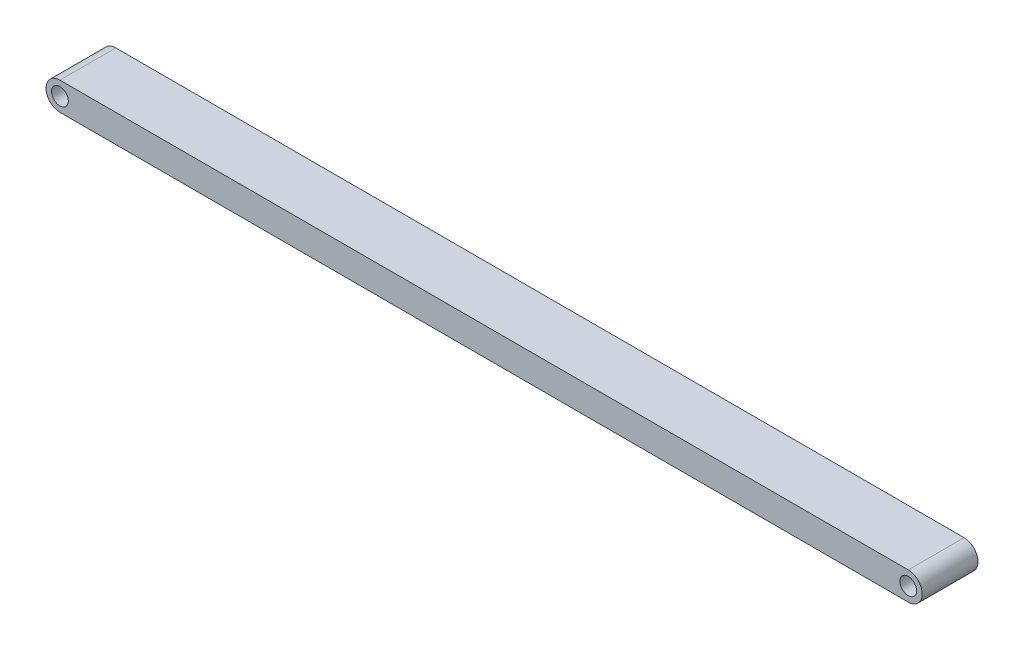
SolidWorks part; units mm, degrees
ref_plane "Plan de face" through (0, 0, 0) normal (0, 0, 1) x (1, 0, 0)
ref_plane "Plan de dessus" through (0, 0, 0) normal (0, 1, 0) x (1, 0, 0)
ref_plane "Plan de droite" through (0, 0, 0) normal (1, 0, 0) x (0, 0, -1)
sketch "Esquisse1" plane through (0, 0, 0) normal (0, 0, 1) x (1, 0, 0)
  line L1 (0, 0) -> (152, 0)
  line L3 (0, 5) -> (152, 5)
  arc A0 (0, 5) -> (0, 0) centre (0, 2.5) ccw
  arc A1 (152, 5) -> (152, 0) centre (152, 2.5) cw
  circle A2 centre (0, 2.5) radius 1.5
  circle A3 centre (152, 2.5) radius 1.5
  dimension "D1" = 3
  dimension "D2" = 3
  dimension "D3" = 5
  dimension "D4" = 152
extrude "Boss.-Extru.1" add sketch "Esquisse1" along normal blind 10
